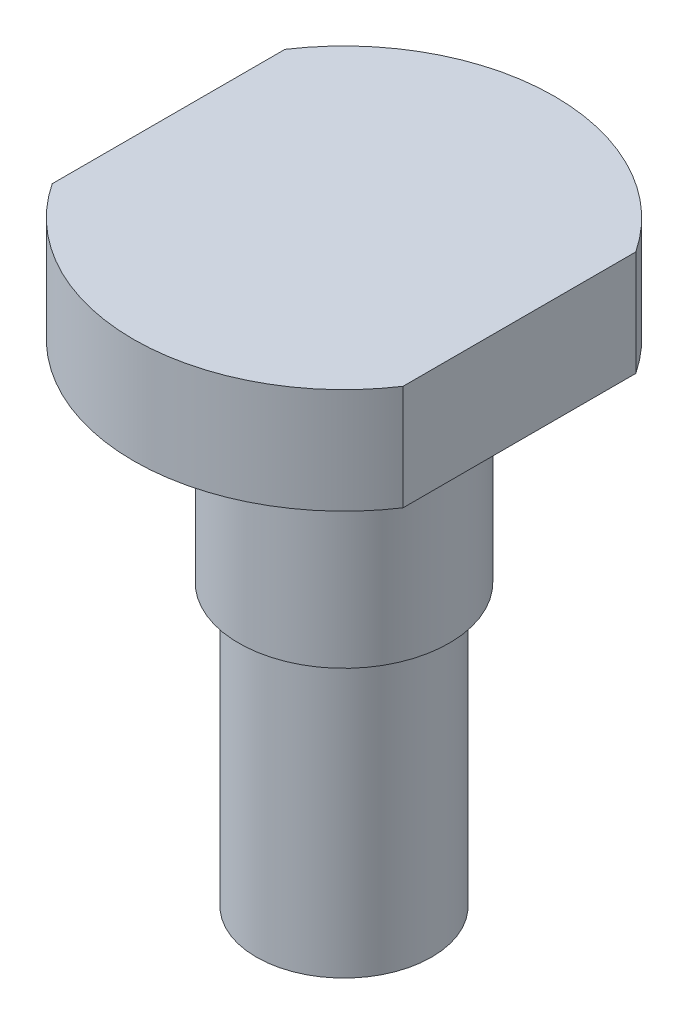
SolidWorks part; units mm, degrees
ref_plane "前视基准面" through (0, 0, 0) normal (0, 0, 1) x (1, 0, 0)
ref_plane "上视基准面" through (0, 0, 0) normal (0, 1, 0) x (1, 0, 0)
ref_plane "右视基准面" through (0, 0, 0) normal (1, 0, 0) x (0, 0, -1)
sketch "草图1" plane through (0, 0, 0) normal (1, 0, 0) x (0, 0, -1)
  line L0 (0, 0) -> (0, 24.9721) construction
  line L1 (0, 0) -> (2.5, 0)
  line L2 (2.5, 0) -> (2.5, 8)
  line L3 (2.5, 8) -> (3, 8)
  line L4 (3, 8) -> (3, 14)
  line L5 (3, 14) -> (6, 14)
  line L6 (6, 14) -> (6, 17)
  line L7 (6, 17) -> (0, 17)
  line L8 (0, 17) -> (0, 0)
  dimension "D1" = 5
  dimension "D2" = 6
  dimension "D3" = 12
  dimension "D4" = 8
  dimension "D5" = 6
  dimension "D6" = 3
revolve "旋转1" add sketch "草图1" angle 360 about L0
sketch "草图2" plane through (0, 17, 0) normal (0, 1, 0) x (1, 0, 0)
  line L0 (0, 0) -> (-7.0367, 0) construction
  line L1 (0, 0) -> (0, 6.7521) construction
  line L2 (-5, -4) -> (-7, -4)
  line L3 (-5, -4) -> (-5, 4)
  line L4 (-5, 4) -> (-7, 4)
  line L5 (-7, -4) -> (-7, 4)
  line L6 (-5, -4) -> (-7, 4) construction
  line L7 (-5, 4) -> (-7, -4) construction
  line L8 (5, -4) -> (7, 4) construction
  line L9 (5, -4) -> (7, -4)
  line L10 (5, -4) -> (5, 4)
  line L11 (5, 4) -> (7, -4) construction
  line L12 (7, -4) -> (7, 4)
  line L13 (5, 4) -> (7, 4)
  point P3 (-6, 0)
  dimension "D1" = 5
  dimension "D2" = 2
  dimension "D3" = 8
extrude "切除-拉伸1" cut sketch "草图2" against normal blind 10
